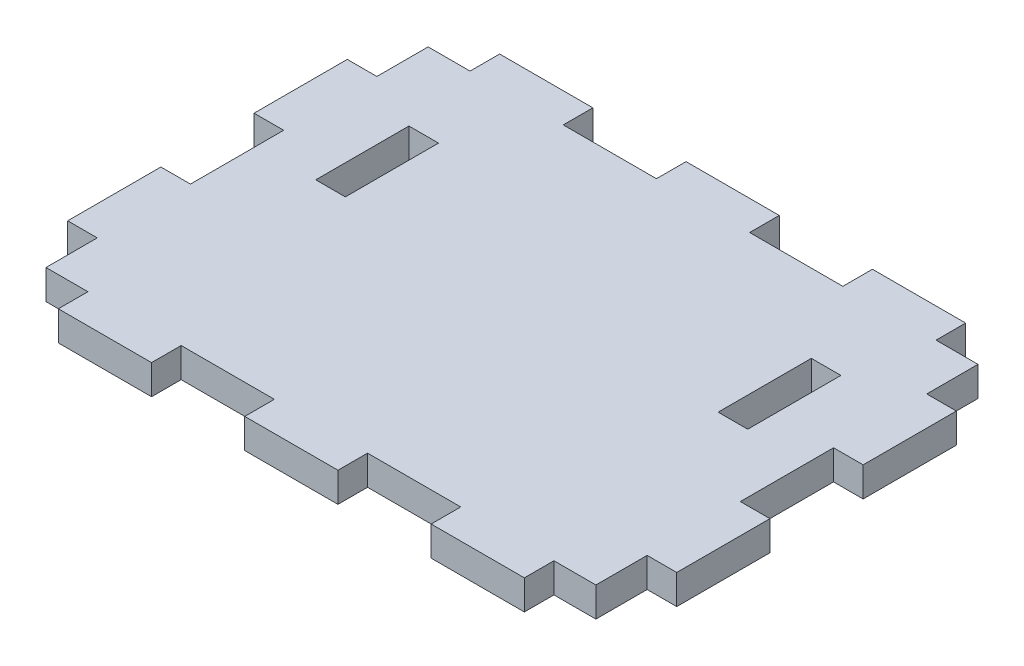
SolidWorks part; units mm, degrees
ref_plane "Front Plane" through (0, 0, 0) normal (0, 0, 1) x (1, 0, 0)
ref_plane "Top Plane" through (0, 0, 0) normal (0, 1, 0) x (1, 0, 0)
ref_plane "Right Plane" through (0, 0, 0) normal (1, 0, 0) x (0, 0, -1)
sketch "Sketch1" plane through (0, 0, 0) normal (0, 1, 0) x (1, 0, 0)
  line L1 (0, 0) -> (65.35, 0)
  line L2 (0, 0) -> (0, 47.35)
  line L3 (0, 47.35) -> (65.35, 47.35)
  line L4 (65.35, 0) -> (65.35, 47.35)
  dimension "D1" = 65.35
  dimension "D2" = 47.35
extrude "Boss-Extrude1" add sketch "Sketch1" along normal blind 3.175
sketch "Sketch2" plane through (0, 0, 0) normal (0, -1, 0) x (1, 0, 0)
  line L0 (65.35, 0) -> (65.35, -47.35) construction
  line L1 (62.175, -38.675) -> (65.35, -38.675)
  line L2 (62.175, -38.675) -> (62.175, -47.35)
  line L3 (62.175, -47.35) -> (65.35, -47.35)
  line L4 (65.35, -38.675) -> (65.35, -47.35)
  line L5 (0, 0) -> (65.35, 0) construction
  line L6 (62.175, -28.675) -> (65.35, -28.675)
  line L7 (62.175, -28.675) -> (62.175, -18.675)
  line L8 (62.175, -18.675) -> (65.35, -18.675)
  line L9 (65.35, -28.675) -> (65.35, -18.675)
  line L10 (62.175, -8.675) -> (65.35, -8.675)
  line L11 (62.175, -8.675) -> (62.175, 0)
  line L12 (62.175, 0) -> (65.35, 0)
  line L13 (65.35, -8.675) -> (65.35, 0)
  line L14 (65.35, -47.35) -> (0, -47.35) construction
  line L15 (0, -47.35) -> (0, 0) construction
  line L16 (0, -47.35) -> (3.175, -47.35)
  line L17 (0, -47.35) -> (0, -38.675)
  line L18 (0, -38.675) -> (3.175, -38.675)
  line L19 (3.175, -47.35) -> (3.175, -38.675)
  line L21 (0, -28.675) -> (3.175, -28.675)
  line L22 (0, -28.675) -> (0, -18.675)
  line L23 (0, -18.675) -> (3.175, -18.675)
  line L24 (3.175, -28.675) -> (3.175, -18.675)
  line L25 (0, 0) -> (3.175, 0)
  line L26 (0, 0) -> (0, -8.675)
  line L27 (0, -8.675) -> (3.175, -8.675)
  line L28 (3.175, 0) -> (3.175, -8.675)
  line L29 (62.175, -47.35) -> (57.675, -47.35)
  line L30 (62.175, -47.35) -> (62.175, -44.175)
  line L31 (62.175, -44.175) -> (57.675, -44.175)
  line L32 (57.675, -47.35) -> (57.675, -44.175)
  line L33 (47.675, -47.35) -> (37.675, -47.35)
  line L34 (47.675, -47.35) -> (47.675, -44.175)
  line L35 (47.675, -44.175) -> (37.675, -44.175)
  line L36 (37.675, -47.35) -> (37.675, -44.175)
  line L37 (27.675, -47.35) -> (17.675, -47.35)
  line L38 (27.675, -47.35) -> (27.675, -44.175)
  line L39 (27.675, -44.175) -> (17.675, -44.175)
  line L40 (17.675, -47.35) -> (17.675, -44.175)
  line L41 (3.175, -47.35) -> (7.675, -47.35)
  line L42 (3.175, -47.35) -> (3.175, -44.175)
  line L43 (3.175, -44.175) -> (7.675, -44.175)
  line L44 (7.675, -47.35) -> (7.675, -44.175)
  line L45 (57.675, -3.175) -> (62.175, -3.175)
  line L46 (57.675, -3.175) -> (57.675, 0)
  line L47 (57.675, 0) -> (62.175, 0)
  line L48 (62.175, -3.175) -> (62.175, 0)
  line L49 (47.675, -3.175) -> (37.675, -3.175)
  line L50 (47.675, -3.175) -> (47.675, 0)
  line L51 (47.675, 0) -> (37.675, 0)
  line L52 (37.675, -3.175) -> (37.675, 0)
  line L53 (27.675, -3.175) -> (17.675, -3.175)
  line L54 (27.675, -3.175) -> (27.675, 0)
  line L55 (27.675, 0) -> (17.675, 0)
  line L56 (17.675, -3.175) -> (17.675, 0)
  line L57 (7.675, -3.175) -> (3.175, -3.175)
  line L58 (7.675, -3.175) -> (7.675, 0)
  line L59 (7.675, 0) -> (3.175, 0)
  line L60 (3.175, -3.175) -> (3.175, 0)
  point P16 (65.35, -23.675)
  point P17 (62.175, -23.675)
  line M30 (0, 0) -> (0, -47.35)
  line M31 (0, -47.35) -> (65.35, -47.35)
  line M32 (65.35, -47.35) -> (65.35, 0)
  line M33 (65.35, 0) -> (0, 0)
  dimension "D1" = 10
  dimension "D2" = 10
  dimension "D3" = 10
  dimension "D4" = 3.175
  dimension "D5" = 3.175
  dimension "D6" = 10
  dimension "D7" = 10
  dimension "D8" = 10
  dimension "D9" = 10
  dimension "D10" = 10
  dimension "D11" = 3.175
  dimension "D12" = 3.175
extrude "Cut-Extrude1" cut sketch "Sketch2" against normal through all contours L32 L2 L31 M31 | L1 L2 M31 M32 | L8 L7 L6 M32 | L11 L10 M32 M33 | L46 L45 L11 M33 | L52 L49 L50 M33 | L36 L34 L35 M31 | L40 L38 L39 M31 | L44 L43 L19 M31 | L19 L18 M31 M30 | L21 L24 L23 M30 | L28 L27 M33 M30 | L57 L58 L28 M33 | L56 L53 L54 M33
sketch "Sketch3" plane through (0, 0, 0) normal (0, -1, 0) x (1, 0, 0)
  line L1 (52.675, -25.7915) -> (55.85, -25.7915)
  line L2 (52.675, -25.7915) -> (52.675, -35.7915)
  line L3 (52.675, -35.7915) -> (55.85, -35.7915)
  line L4 (55.85, -25.7915) -> (55.85, -35.7915)
  line L5 (12.675, -25.7915) -> (9.5, -25.7915)
  line L6 (12.675, -25.7915) -> (12.675, -35.7915)
  line L7 (12.675, -35.7915) -> (9.5, -35.7915)
  line L8 (9.5, -25.7915) -> (9.5, -35.7915)
extrude "Cut-Extrude2" cut sketch "Sketch3" against normal through all
